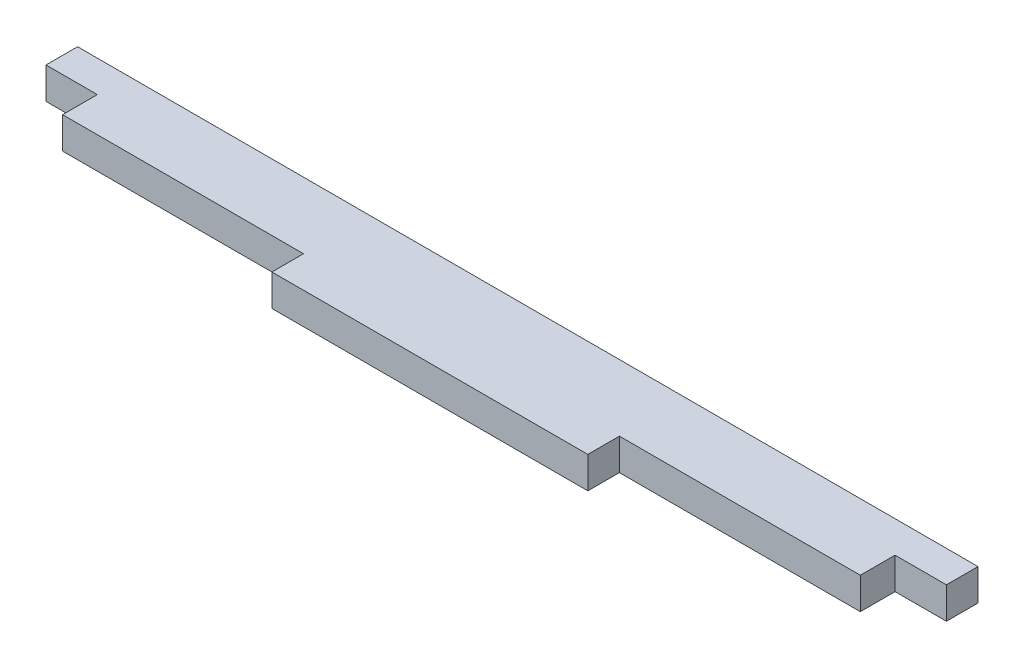
SolidWorks part; units mm, degrees
ref_plane "Front Plane" through (0, 0, 0) normal (0, 0, 1) x (1, 0, 0)
ref_plane "Top Plane" through (0, 0, 0) normal (0, 1, 0) x (1, 0, 0)
ref_plane "Right Plane" through (0, 0, 0) normal (1, 0, 0) x (0, 0, -1)
sketch "Sketch1" plane through (0, 0, 0) normal (0, 1, 0) x (1, 0, 0)
  line L0 (-25.25, 2) -> (-10, 2)
  line L1 (-10, 2) -> (-10, 0)
  line L2 (-10, 0) -> (10, 0)
  line L3 (10, 0) -> (10, 2)
  line L4 (10, 2) -> (25.25, 2)
  line L5 (25.25, 2) -> (25.25, 4.2)
  line L6 (25.25, 4.2) -> (28.5, 4.2)
  line L7 (28.5, 4.2) -> (28.5, 6.2)
  line L8 (28.5, 6.2) -> (-28.5, 6.2)
  line L9 (-28.5, 6.2) -> (-28.5, 4.2)
  line L10 (-28.5, 4.2) -> (-25.25, 4.2)
  line L11 (-25.25, 4.2) -> (-25.25, 2)
  dimension "D1" = 57
  dimension "D2" = 50.5
  dimension "D3" = 2.2
  dimension "D4" = 2
  dimension "D5" = 20
  dimension "D6" = 2
extrude "Boss-Extrude1" add sketch "Sketch1" along normal blind 2
